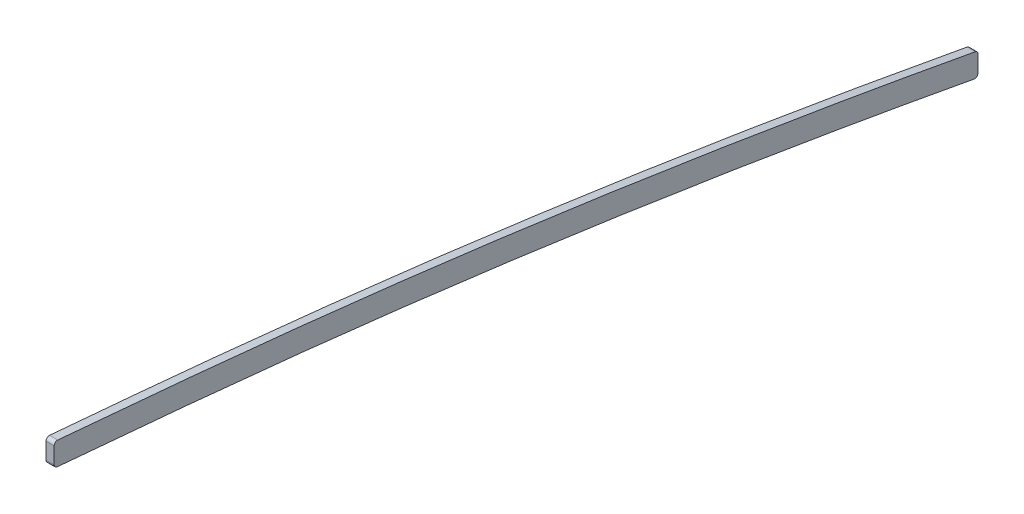
SolidWorks part; units mm, degrees
material "Plywood"
ref_plane "Front Plane" through (0, 0, 0) normal (0, 0, 1) x (1, 0, 0)
ref_plane "Top Plane" through (0, 0, 0) normal (0, 1, 0) x (1, 0, 0)
ref_plane "Right Plane" through (0, 0, 0) normal (1, 0, 0) x (0, 0, -1)
sketch "Sketch2" plane through (0, 0, 0) normal (1, 0, 0) x (0, 0, -1)
  line L0 (2794, -12.7) -> (0, -12.7)
  line L1 (0, 12.7) -> (2794, 12.7)
  line L2 (0, -12.7) -> (0, 12.7)
  line L3 (99.06, 65.345) -> (99.06, 75.0357)
  line L4 (2669.54, 30.4321) -> (2669.54, 39.4761)
  line L5 (2311.4, 87.2885) -> (2311.4, 78.3664)
  arc A0 (47.6236, 51.8639) -> (46.17, 51.0862) centre (81.3294, -12.8832) ccw
  arc A1 (46.17, 51.0862) -> (42.454, 48.8983) centre (81.3033, -12.8358) ccw
  arc A2 (604.515, 139.4337) -> (596.5837, 139.4794) centre (529.8377, -12134.2803) ccw
  arc A3 (50.452, 43.2954) -> (47.189, 41.3742) centre (81.3033, -12.8358) ccw
  arc A4 (51.7287, 43.9784) -> (50.452, 43.2954) centre (81.3294, -12.8832) ccw
  arc A5 (604.4609, 130.5438) -> (596.5354, 130.5895) centre (529.8377, -12134.2803) ccw
  spline S0 degree 3 poles (42.454, 48.8983) (38.8087, 46.6043) (35.3922, 44.0059) (29.013, 38.2192) (26.0797, 35.0549) (23.4257, 31.6631) knots 0 0 0 0 0.5 0.5 1 1 1 1
  spline S1 degree 3 poles (50.6762, 53.3638) (49.647, 52.8875) (48.6295, 52.3876) (47.6236, 51.8639) knots 0 0 0 0 1 1 1 1
  spline S2 degree 3 poles (50.6762, 53.3638) (57.4619, 56.5022) (64.2646, 59.6027) (77.8982, 65.7412) (84.7292, 68.779) (91.5775, 71.7785) knots 0 0 0 0 0.5 0.5 1 1 1 1
  spline S3 degree 3 poles (135.1572, 90.0546) (146.0437, 94.3752) (156.9989, 98.5043) (173.5662, 104.3226) (179.1109, 106.1998) (190.2486, 109.8197) (195.8415, 111.5623) (207.0655, 114.9013) (212.698, 116.4984) (224.006, 119.5405) (229.6832, 120.9862) (246.7672, 125.0777) (258.2252, 127.4823) (269.7699, 129.479) knots 0 0 0 0 0.25 0.25 0.375 0.375 0.5 0.5 0.625 0.625 0.75 0.75 1 1 1 1
  spline S4 degree 3 poles (107.0497, 78.4661) (116.3733, 82.4386) (125.7374, 86.3161) (135.1572, 90.0546) knots 0 0 0 0 1 1 1 1
  spline S5 degree 3 poles (91.5775, 71.7785) (94.2324, 72.9414) (98.1371, 74.6408) (103.2975, 76.8633) (105.7985, 77.9329) (107.0497, 78.4661) knots 0 0 0 0 0.515864 0.757931 1 1 1 1
  spline S6 degree 3 poles (269.7699, 129.479) (274.1234, 130.2319) (278.4857, 130.9259) (287.228, 132.196) (291.6086, 132.772) (300.3818, 133.8184) (304.7746, 134.289) (313.5678, 135.1544) (317.9679, 135.5494) (322.3695, 135.9285) knots 0 0 0 0 0.25 0.25 0.5 0.5 0.75 0.75 1 1 1 1
  spline S7 degree 3 poles (322.3695, 135.9285) (327.0734, 136.3334) (331.7813, 136.6898) (336.4922, 137.003) knots 0 0 0 0 1 1 1 1
  spline S8 degree 3 poles (1110.4182, 139.2745) (1129.952, 139.2456) (1149.4859, 139.212) (1188.5536, 139.1159) (1208.0873, 139.0527) (1227.621, 138.955) knots 0 0 0 0 0.5 0.5 1 1 1 1
  spline S9 degree 3 poles (336.4922, 137.003) (349.7829, 137.8865) (363.0943, 138.4237) (376.4101, 138.754) knots 0 0 0 0 1 1 1 1
  spline S10 degree 3 poles (768.7401, 138.4684) (782.9768, 138.4603) (797.2135, 138.4795) (825.6867, 138.5497) (839.9233, 138.6001) (868.3963, 138.719) (882.6328, 138.7896) (911.1057, 138.9396) (925.3422, 139.0185) (953.8152, 139.1601) (968.0517, 139.2222) (996.5249, 139.31) (1010.7616, 139.335) (1039.2349, 139.3496) (1053.4716, 139.3405) (1081.9449, 139.3137) (1096.1815, 139.2957) (1110.4182, 139.2745) knots 0 0 0 0 0.125 0.125 0.25 0.25 0.375 0.375 0.5 0.5 0.625 0.625 0.75 0.75 0.875 0.875 1 1 1 1
  spline S11 degree 3 poles (376.4101, 138.754) (383.7263, 138.9356) (391.0438, 139.0556) (405.6796, 139.2242) (412.9979, 139.2729) (420.3162, 139.3058) knots 0 0 0 0 0.5 0.5 1 1 1 1
  spline S12 degree 3 poles (630.7784, 139.2514) (653.7718, 139.0753) (676.765, 138.8717) (711.2553, 138.6477) (722.7522, 138.5862) (745.7461, 138.4998) (757.2431, 138.475) (768.7401, 138.4684) knots 0 0 0 0 0.5 0.5 0.75 0.75 1 1 1 1
  spline S13 degree 3 poles (420.3162, 139.3058) (422.4132, 139.3152) (426.3958, 139.3304) (430.3784, 139.3421) (432.2639, 139.3471) knots 0 0 0 0 0.526549 1 1 1 1
  spline S14 degree 3 poles (604.515, 139.4337) (609.9407, 139.4007) (618.6952, 139.3421) (627.4497, 139.2769) (630.7784, 139.2514) knots 0 0 0 0 0.619766 1 1 1 1
  spline S15 degree 3 poles (432.2639, 139.3471) (433.5536, 139.3506) (434.8433, 139.3539) (436.133, 139.3572) knots 0 0 0 0 1 1 1 1
  spline S16 degree 3 poles (436.133, 139.3572) (449.5039, 139.3907) (462.8749, 139.4124) (489.6167, 139.4986) (502.9875, 139.5591) (529.7293, 139.628) (543.1002, 139.6392) (569.8421, 139.601) (583.213, 139.552) (596.5837, 139.4794) knots 0 0 0 0 0.25 0.25 0.5 0.5 0.75 0.75 1 1 1 1
  spline S17 degree 3 poles (1227.621, 138.955) (1248.8073, 138.8489) (1269.9936, 138.7012) (1312.3638, 138.2707) (1333.5477, 137.9874) (1375.9124, 137.2493) (1397.0931, 136.7926) (1439.4513, 135.7019) (1460.629, 135.0692) (1502.9791, 133.6705) (1524.1522, 132.9074) (1566.4943, 131.2847) (1587.6632, 130.4232) (1651.1641, 127.7091) (1693.4904, 125.7283) (1735.8113, 123.6237) knots 0 0 0 0 0.125 0.125 0.25 0.25 0.375 0.375 0.5 0.5 0.625 0.625 0.75 0.75 1 1 1 1
  spline S18 degree 3 poles (1735.8113, 123.6237) (1776.1386, 121.6183) (1816.4603, 119.5006) (1897.0937, 115.0876) (1937.4056, 112.793) (2018.0184, 108.0184) (2058.3195, 105.5391) (2138.9038, 100.3072) (2179.1874, 97.5551) (2239.587, 93.0802) (2259.7163, 91.5298) (2289.9004, 89.0908) (2299.9602, 88.2588) (2320.076, 86.5529) (2330.1321, 85.679) (2350.2394, 83.8743) (2360.2905, 82.9433) (2380.386, 81.0032) (2390.4301, 79.9934) (2420.547, 76.8276) (2440.6065, 74.5337) (2480.6756, 69.5563) (2500.6872, 66.8742) (2540.6543, 61.1502) (2560.611, 58.1098) (2600.4755, 51.7025) (2620.383, 48.3375) (2650.1996, 43.0417) (2660.1312, 41.2345) (2679.9761, 37.5259) (2689.8897, 35.6246) (2699.7923, 33.6648) knots 0 0 0 0 0.125 0.125 0.25 0.25 0.375 0.375 0.5 0.5 0.5625 0.5625 0.59375 0.59375 0.625 0.625 0.65625 0.65625 0.6875 0.6875 0.75 0.75 0.8125 0.8125 0.875 0.875 0.9375 0.9375 0.96875 0.96875 1 1 1 1
  spline S19 degree 1 poles (47.189, 41.3742) (30.427, 26.1847) knots 0 0 1 1 construction
  spline S20 degree 1 poles (54.4091, 45.2955) (51.7287, 43.9784) knots 0 0 1 1 construction
  spline S21 degree 1 poles (54.4091, 45.2955) (95.1442, 63.6354) knots 0 0 1 1 construction
  spline S22 degree 1 poles (95.1442, 63.6354) (110.5345, 70.2875) knots 0 0 1 1 construction
  spline S23 degree 1 poles (110.5345, 70.2875) (138.4366, 81.7916) knots 0 0 1 1 construction
  spline S24 degree 1 poles (138.4366, 81.7916) (271.285, 120.719) knots 0 0 1 1 construction
  spline S25 degree 1 poles (271.285, 120.719) (323.1321, 127.0712) knots 0 0 1 1 construction
  spline S26 degree 1 poles (323.1321, 127.0712) (337.0819, 128.1326) knots 0 0 1 1 construction
  spline S27 degree 1 poles (337.0819, 128.1326) (376.6306, 129.8668) knots 0 0 1 1 construction
  spline S28 degree 1 poles (376.6306, 129.8668) (420.3562, 130.4159) knots 0 0 1 1 construction
  spline S29 degree 1 poles (420.3562, 130.4159) (432.2877, 130.4571) knots 0 0 1 1 construction
  spline S30 degree 1 poles (432.2877, 130.4571) (436.1553, 130.4672) knots 0 0 1 1 construction
  spline S31 degree 1 poles (436.1553, 130.4672) (596.5354, 130.5895) knots 0 0 1 1 construction
  spline S32 degree 1 poles (604.4609, 130.5438) (630.7103, 130.3617) knots 0 0 1 1 construction
  spline S33 degree 1 poles (630.7103, 130.3617) (768.735, 129.5784) knots 0 0 1 1 construction
  spline S34 degree 1 poles (768.735, 129.5784) (1110.405, 130.3845) knots 0 0 1 1 construction
  spline S35 degree 1 poles (1110.405, 130.3845) (1227.5765, 130.0651) knots 0 0 1 1 construction
  spline S36 degree 1 poles (1227.5765, 130.0651) (1735.3698, 114.7447) knots 0 0 1 1 construction
  spline S37 degree 1 poles (1735.3698, 114.7447) (2698.0664, 24.9439) knots 0 0 1 1 construction
  spline S38 degree 3 poles (30.427, 26.1847) (31.5989, 27.6824) (34.071, 30.5835) (38.124, 34.5916) (42.486, 38.2181) (45.592, 40.3693) (47.189, 41.3742) knots -0.000002 -0.000002 -0.000002 -0.000002 0.249999 0.499999 0.75 1 1 1 1
  spline S39 degree 3 poles (51.7287, 43.9784) (51.9494, 44.0933) (52.3923, 44.3206) (53.0604, 44.6537) (53.7324, 44.9791) (54.1832, 45.1909) (54.4091, 45.2955) knots 0.000384 0.000384 0.000384 0.000384 0.25029 0.500196 0.750102 1.000008 1.000008 1.000008 1.000008
  spline S40 degree 3 poles (54.4091, 45.2955) (57.7875, 46.858) (64.5519, 49.9638) (74.7284, 54.5738) (84.9254, 59.1368) (91.7348, 62.1421) (95.1442, 63.6354) knots 0.000027 0.000027 0.000027 0.000027 0.250021 0.500014 0.750007 1 1 1 1
  spline S41 degree 3 poles (95.1442, 63.6354) (96.1287, 64.0666) (97.7542, 64.7769) (100.3172, 65.8923) (103.1775, 67.132) (106.6816, 68.6417) (109.2496, 69.74) (110.5345, 70.2875) knots 0 0 0 0 0.192239 0.317239 0.5 0.75 1 1 1 1
  spline S42 degree 3 poles (110.5345, 70.2875) (112.8507, 71.2744) (117.4893, 73.2368) (124.4567, 76.1381) (131.4385, 78.9943) (136.1012, 80.8648) (138.4366, 81.7916) knots 0 0 0 0 0.25 0.5 0.75 1 1 1 1
  spline S43 degree 3 poles (138.4366, 81.7916) (143.8269, 83.9309) (154.6523, 88.1188) (176.4082, 96.0376) (203.9068, 104.9982) (237.3947, 114.0271) (259.9348, 118.756) (271.285, 120.719) knots 0 0 0 0 0.125 0.25 0.5 0.75 1 1 1 1
  spline S44 degree 3 poles (271.285, 120.719) (275.5587, 121.4581) (284.1243, 122.8211) (297.0364, 124.5189) (310.0184, 125.9099) (318.7666, 126.6953) (323.1321, 127.0712) knots 0 0 0 0 0.249999 0.499998 0.749998 0.999997 0.999997 0.999997 0.999997
  spline S45 degree 3 poles (323.1321, 127.0712) (324.2931, 127.1712) (326.6152, 127.365) (330.1016, 127.6385) (333.5902, 127.8951) (335.918, 128.0552) (337.0819, 128.1326) knots 0.000012 0.000012 0.000012 0.000012 0.250009 0.500006 0.750003 1 1 1 1
  spline S46 degree 3 poles (337.0819, 128.1326) (340.3679, 128.351) (346.9399, 128.7449) (356.8213, 129.2212) (366.7163, 129.5951) (373.3266, 129.7848) (376.6306, 129.8668) knots 0 0 0 0 0.25 0.5 0.75 1 1 1 1
  spline S47 degree 3 poles (376.6306, 129.8668) (380.2664, 129.957) (387.5348, 130.1068) (398.4622, 130.2594) (409.401, 130.3587) (416.7054, 130.3994) (420.3562, 130.4159) knots 0 0 0 0 0.25 0.5 0.75 1 1 1 1
  spline S48 degree 3 poles (420.3562, 130.4159) (421.35, 130.4203) (423.3375, 130.4286) (426.3202, 130.4394) (429.3035, 130.4489) (431.293, 130.4545) (432.2877, 130.4571) knots 0 0 0 0 0.25 0.5 0.75 1 1 1 1
  spline S49 degree 3 poles (432.2877, 130.4571) (432.61, 130.458) (433.2547, 130.4597) (434.2216, 130.4623) (435.1885, 130.4648) (435.833, 130.4664) (436.1553, 130.4672) knots 0 0 0 0 0.25 0.5 0.75 1 1 1 1
  spline S50 degree 3 poles (436.1553, 130.4672) (449.5283, 130.5007) (476.2757, 130.5466) (516.389, 130.7288) (556.4563, 130.7597) (583.1765, 130.6621) (596.5354, 130.5895) knots 0 0 0 0 0.25 0.5 0.75 1 1 1 1
  spline S51 degree 3 poles (604.4609, 130.5438) (606.6482, 130.5306) (611.0225, 130.5029) (617.5847, 130.4584) (624.1472, 130.4113) (628.5227, 130.3785) (630.7103, 130.3617) knots -0.000001 -0.000001 -0.000001 -0.000001 0.249999 0.5 0.75 1 1 1 1
  spline S52 degree 3 poles (630.7103, 130.3617) (642.2061, 130.2736) (665.1936, 130.0838) (699.6991, 129.8192) (734.215, 129.6347) (757.2286, 129.585) (768.735, 129.5784) knots 0 0 0 0 0.25 0.5 0.75 1 1 1 1
  spline S53 degree 3 poles (768.735, 129.5784) (797.2224, 129.5621) (854.2037, 129.7251) (939.6352, 130.2366) (1024.993, 130.5249) (1081.9376, 130.4268) (1110.405, 130.3845) knots 0 0 0 0 0.25 0.5 0.75 1 1 1 1
  spline S54 degree 3 poles (1110.405, 130.3845) (1120.1708, 130.3701) (1139.7031, 130.3388) (1168.9984, 130.2777) (1198.2906, 130.1944) (1217.8142, 130.1139) (1227.5765, 130.0651) knots 0 0 0 0 0.25 0.5 0.75 1 1 1 1
  spline S55 degree 3 poles (1227.5765, 130.0651) (1269.9112, 129.8532) (1333.4277, 129.2734) (1418.0422, 127.4491) (1502.666, 124.9136) (1608.4542, 120.8033) (1693.0701, 116.8482) (1735.3698, 114.7447) knots 0 0 0 0 0.25 0.375 0.5 0.75 1 1 1 1
  spline S56 degree 3 poles (1735.3698, 114.7447) (1815.9959, 110.7352) (1936.9067, 104.0964) (2098.0495, 94.188) (2198.6947, 87.3146) (2264.7604, 82.2221) (2300.6441, 79.2861) (2321.4466, 77.5184) (2355.8702, 74.4619) (2400.272, 70.2017) (2479.5705, 61.1274) (2559.2921, 49.6509) (2626.7976, 38.2355) (2659.2727, 32.3571) (2679.0625, 28.6522) (2690.9404, 26.3542) (2698.0664, 24.9439) knots 0 0 0 0 0.25 0.375 0.5 0.5625 0.580337 0.611587 0.627212 0.6875 0.75 0.875 0.9375 0.962411 0.977446 1 1 1 1
  dimension "D1" = 25.4
  dimension "D2" = 8.89
  dimension "D3" = 99.06
  dimension "D4" = 2669.54
  dimension "D5" = 2311.4
extrude "Boss-Extrude1" add sketch "Sketch2" against normal mid plane 3.175 contours L5 S56 L4 S18
fillet "Fillet1" radius 1.27 4 edges at (0, 78.3664, -2311.4) (0, 30.4321, -2669.54)
